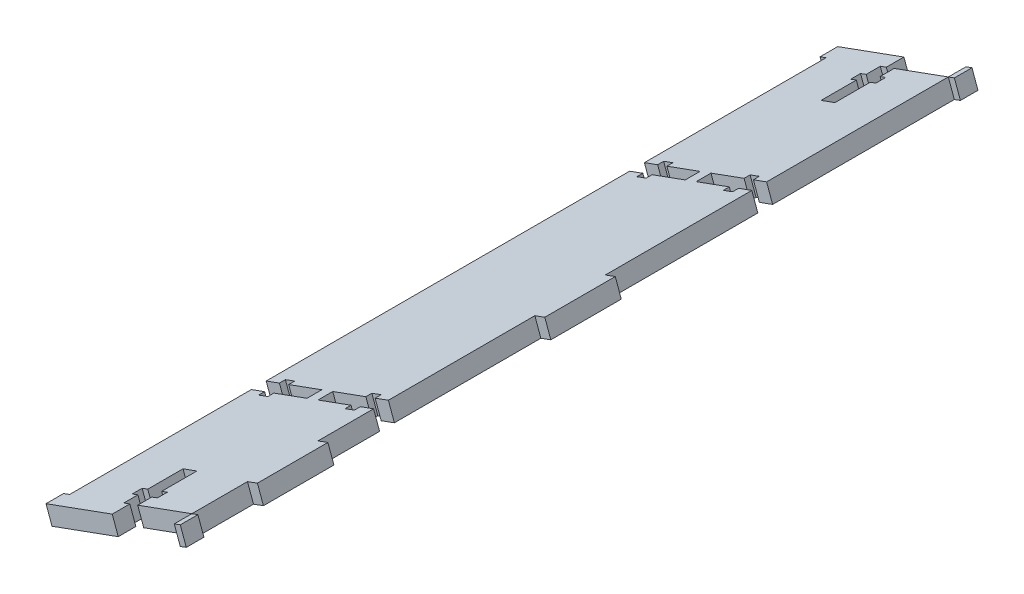
SolidWorks part; units mm, degrees
ref_plane "Front Plane" through (0, 0, 0) normal (0, 0, 1) x (1, 0, 0)
ref_plane "Top Plane" through (0, 0, 0) normal (0, 1, 0) x (1, 0, 0)
ref_plane "Right Plane" through (0, 0, 0) normal (1, 0, 0) x (0, 0, -1)
sketch "Sketch2" plane through (0, 0, 4.9494) normal (0, 0, 1) x (1, 0, 0)
  line L12 (-9.2679, -20.9726) -> (-91.5172, -50.8831) construction
  line L17 (-52.9615, -36.8621) -> (-51.2527, -41.561)
  line L18 (-52.9615, -36.8621) -> (-87.6455, -49.4751)
  line L19 (-51.2527, -41.561) -> (-85.9367, -54.1741)
  line L20 (-87.6455, -49.4751) -> (-85.9367, -54.1741)
  line L24 (-75.9608, -81.6065) -> (-64.6827, -112.6194) construction
  dimension "D1" = 5
extrude "Boss-Extrude1" add sketch "Sketch2" along normal up to surface (214.6865 mm away)
sketch "Sketch4" plane through (7.3623, -20.2452, 0) normal (0.3418, -0.9398, 0) x (-0.9398, -0.3418, 0)
  line L0 (78.7237, -4.9494) -> (82.9237, -4.9494)
  line L1 (78.7237, -4.9494) -> (78.7237, -8.9494)
  line L2 (82.9237, -4.9494) -> (82.9237, -8.9494)
  line L3 (77.0237, -8.9494) -> (78.7237, -8.9494)
  line L4 (77.0237, -8.9494) -> (77.0237, -11.7494)
  line L5 (84.6237, -8.9494) -> (84.6237, -11.7494)
  line L6 (77.0237, -11.7494) -> (78.7237, -11.7494)
  line L7 (78.7237, -11.7494) -> (78.7237, -21.7494)
  line L8 (82.9237, -11.7494) -> (82.9237, -21.7494)
  line L9 (78.7237, -21.7494) -> (82.9237, -21.7494)
  line L10 (82.9237, -11.7494) -> (84.6237, -11.7494)
  line L11 (82.9237, -8.9494) -> (84.6237, -8.9494)
  line L14 (62.3706, -60.721) -> (62.3706, -56.521)
  line L25 (62.3706, -4.9494) -> (99.2768, -4.9494) construction
  line L26 (82.9237, -219.6358) -> (78.7237, -219.6358)
  line L27 (82.9237, -219.6358) -> (82.9237, -215.6358)
  line L28 (80.8237, -21.7494) -> (80.8237, -4.9494) construction
  line L29 (78.7237, -219.6358) -> (78.7237, -215.6358)
  line L30 (84.6237, -215.6358) -> (82.9237, -215.6358)
  line L31 (84.6237, -215.6358) -> (84.6237, -212.8358)
  line L32 (77.0237, -215.6358) -> (77.0237, -212.8358)
  line L33 (84.6237, -212.8358) -> (82.9237, -212.8358)
  line L34 (82.9237, -212.8358) -> (82.9237, -202.8358)
  line L35 (78.7237, -212.8358) -> (78.7237, -202.8358)
  line L36 (82.9237, -202.8358) -> (78.7237, -202.8358)
  line L37 (78.7237, -212.8358) -> (77.0237, -212.8358)
  line L38 (78.7237, -215.6358) -> (77.0237, -215.6358)
  line L39 (80.8237, -202.8358) -> (80.8237, -219.6358) construction
  line L40 (62.3706, -219.6358) -> (99.2768, -219.6358) construction
  line L41 (62.3706, -60.721) -> (66.3706, -60.721)
  line L42 (62.3706, -56.521) -> (66.3706, -56.521)
  line L43 (66.3706, -62.421) -> (66.3706, -60.721)
  line L44 (66.3706, -62.421) -> (69.1706, -62.421)
  line L45 (66.3706, -54.821) -> (69.1706, -54.821)
  line L46 (69.1706, -62.421) -> (69.1706, -60.721)
  line L47 (69.1706, -60.721) -> (79.1706, -60.721)
  line L48 (69.1706, -56.521) -> (79.1706, -56.521)
  line L49 (79.1706, -60.721) -> (79.1706, -56.521)
  line L50 (69.1706, -56.521) -> (69.1706, -54.821)
  line L51 (66.3706, -56.521) -> (66.3706, -54.821)
  line L52 (79.1706, -58.621) -> (62.3706, -58.621) construction
  line L55 (62.3706, -219.6358) -> (62.3706, -4.9494) construction
  line L56 (62.3706, -4.9494) -> (62.3706, -112.2926) construction
  line L57 (62.3706, -112.2926) -> (99.2768, -112.2926) construction
  line L58 (79.1706, -165.9642) -> (62.3706, -165.9642) construction
  line L59 (66.3706, -168.0642) -> (66.3706, -169.7642)
  line L60 (69.1706, -168.0642) -> (69.1706, -169.7642)
  line L61 (79.1706, -163.8642) -> (79.1706, -168.0642)
  line L62 (69.1706, -168.0642) -> (79.1706, -168.0642)
  line L63 (69.1706, -163.8642) -> (79.1706, -163.8642)
  line L64 (69.1706, -162.1642) -> (69.1706, -163.8642)
  line L65 (66.3706, -169.7642) -> (69.1706, -169.7642)
  line L66 (66.3706, -162.1642) -> (69.1706, -162.1642)
  line L67 (66.3706, -162.1642) -> (66.3706, -163.8642)
  line L68 (62.3706, -168.0642) -> (66.3706, -168.0642)
  line L69 (62.3706, -163.8642) -> (66.3706, -163.8642)
  line L70 (62.3706, -163.8642) -> (62.3706, -168.0642)
  line L76 (99.2768, -219.6358) -> (99.2768, -4.9494) construction
  line L77 (80.8237, -171.4513) -> (80.8237, -40.1199) construction
  line L78 (82.4768, -165.9642) -> (99.2768, -165.9642) construction
  line L87 (99.2768, -4.9494) -> (99.2768, -112.2926) construction
  line L88 (82.4768, -58.621) -> (99.2768, -58.621) construction
  line L89 (99.2768, -163.8642) -> (99.2768, -168.0642)
  line L90 (99.2768, -163.8642) -> (95.2768, -163.8642)
  line L91 (99.2768, -168.0642) -> (95.2768, -168.0642)
  line L92 (95.2768, -162.1642) -> (95.2768, -163.8642)
  line L93 (95.2768, -162.1642) -> (92.4768, -162.1642)
  line L94 (95.2768, -169.7642) -> (92.4768, -169.7642)
  line L95 (92.4768, -162.1642) -> (92.4768, -163.8642)
  line L96 (92.4768, -163.8642) -> (82.4768, -163.8642)
  line L97 (92.4768, -168.0642) -> (82.4768, -168.0642)
  line L98 (82.4768, -163.8642) -> (82.4768, -168.0642)
  line L99 (92.4768, -168.0642) -> (92.4768, -169.7642)
  line L100 (95.2768, -168.0642) -> (95.2768, -169.7642)
  line L101 (95.2768, -56.521) -> (95.2768, -54.821)
  line L102 (92.4768, -56.521) -> (92.4768, -54.821)
  line L103 (82.4768, -60.721) -> (82.4768, -56.521)
  line L104 (92.4768, -56.521) -> (82.4768, -56.521)
  line L105 (92.4768, -60.721) -> (82.4768, -60.721)
  line L106 (92.4768, -62.421) -> (92.4768, -60.721)
  line L107 (95.2768, -54.821) -> (92.4768, -54.821)
  line L108 (95.2768, -62.421) -> (92.4768, -62.421)
  line L109 (95.2768, -62.421) -> (95.2768, -60.721)
  line L110 (99.2768, -56.521) -> (95.2768, -56.521)
  line L111 (99.2768, -60.721) -> (95.2768, -60.721)
  line L112 (99.2768, -60.721) -> (99.2768, -56.521)
  point P70 (80.8237, -112.2926)
  dimension "D1" = 4.2
  dimension "D2" = 1.7
  dimension "D3" = 1.7
  dimension "D4" = 2.8
  dimension "D5" = 10
  dimension "D6" = 4
  dimension "D7" = 4.2
  dimension "D8" = 1.7
  dimension "D9" = 1.7
  dimension "D10" = 2.8
  dimension "D11" = 10
  dimension "D12" = 4
  dimension "D13" = 4.2
  dimension "D14" = 1.7
  dimension "D15" = 1.7
  dimension "D16" = 2.8
  dimension "D17" = 10
  dimension "D18" = 4
extrude "Cut-Extrude3" cut sketch "Sketch4" against normal through all
sketch "Sketch5" plane through (7.3623, -20.2452, 0) normal (0.3418, -0.9398, 0) x (0.9398, 0.3418, 0)
  line L0 (-81.1002, 219.6358) -> (-101.1002, 219.6358)
  line L1 (-81.1002, 219.6358) -> (-81.1002, 224.6358)
  line L2 (-101.1002, 219.6358) -> (-101.1002, 224.6358)
  line L3 (-81.1002, 224.6358) -> (-101.1002, 224.6358)
  line L4 (-99.2768, 219.6358) -> (-82.9237, 219.6358) construction
  line L5 (-60.5471, 219.6358) -> (-80.5471, 219.6358)
  line L6 (-60.5471, 219.6358) -> (-60.5471, 224.6358)
  line L7 (-80.5471, 219.6358) -> (-80.5471, 224.6358)
  line L8 (-60.5471, 224.6358) -> (-80.5471, 224.6358)
  line L9 (-78.7237, 219.6358) -> (-62.3706, 219.6358) construction
  line L10 (-62.3706, 102.2926) -> (-62.3706, 122.2926)
  line L11 (-62.3706, 102.2926) -> (-59.3706, 102.2926)
  line L12 (-62.3706, 122.2926) -> (-59.3706, 122.2926)
  line L13 (-59.3706, 102.2926) -> (-59.3706, 122.2926)
  line L14 (-62.3706, 60.721) -> (-62.3706, 163.8642) construction
  line L15 (-62.3706, 203.85) -> (-62.3706, 183.85)
  line L16 (-62.3706, 203.85) -> (-59.3706, 203.85)
  line L17 (-62.3706, 183.85) -> (-59.3706, 183.85)
  line L18 (-59.3706, 203.85) -> (-59.3706, 183.85)
  line L19 (-62.3706, 168.0642) -> (-62.3706, 219.6358) construction
  line L20 (-62.3706, 425.3148) -> (-62.3706, -200.7297)
  line L24 (-62.3706, 60.721) -> (-62.3706, 163.8642) construction
  line L25 (-101.1002, 4.9494) -> (-81.1002, 4.9494)
  line L26 (-101.1002, 4.9494) -> (-101.1002, -0.0506)
  line L27 (-81.1002, 4.9494) -> (-81.1002, -0.0506)
  line L28 (-101.1002, -0.0506) -> (-81.1002, -0.0506)
  line L29 (-99.2768, 4.9494) -> (-82.9237, 4.9494) construction
  line L30 (-80.5471, 4.9494) -> (-60.5471, 4.9494)
  line L31 (-80.5471, 4.9494) -> (-80.5471, -0.0506)
  line L32 (-60.5471, 4.9494) -> (-60.5471, -0.0506)
  line L33 (-80.5471, -0.0506) -> (-60.5471, -0.0506)
  line L34 (-78.7237, 4.9494) -> (-62.3706, 4.9494) construction
  line L35 (25.2614, 224.6358) -> (-232.1386, 224.6358) construction
  point P10 (-91.1002, 219.6358)
  point P11 (-70.5471, 219.6358)
  point P16 (-62.3706, 112.2926)
  point P23 (-62.3706, 193.85)
  point P31 (-62.3706, 112.2926)
  point P39 (-91.1002, 4.9494)
  point P49 (-70.5471, 4.9494)
  dimension "D2" = 20
  dimension "D4" = 20
  dimension "D5" = 3
  dimension "D6" = 20
  dimension "D7" = 3
  dimension "D8" = 20
  dimension "D11" = 5
  dimension "D12" = 20
  dimension "D13" = 5
  dimension "D14" = 20
extrude "Boss-Extrude2" add sketch "Sketch5" against normal blind 5 contours L31 L33 L32 L30 | L26 L28 L27 L25 | L11 L13 L12 L10 | L18 L16 L15 L17 | L6 L8 L7 L5 | L1 L3 L2 L0
